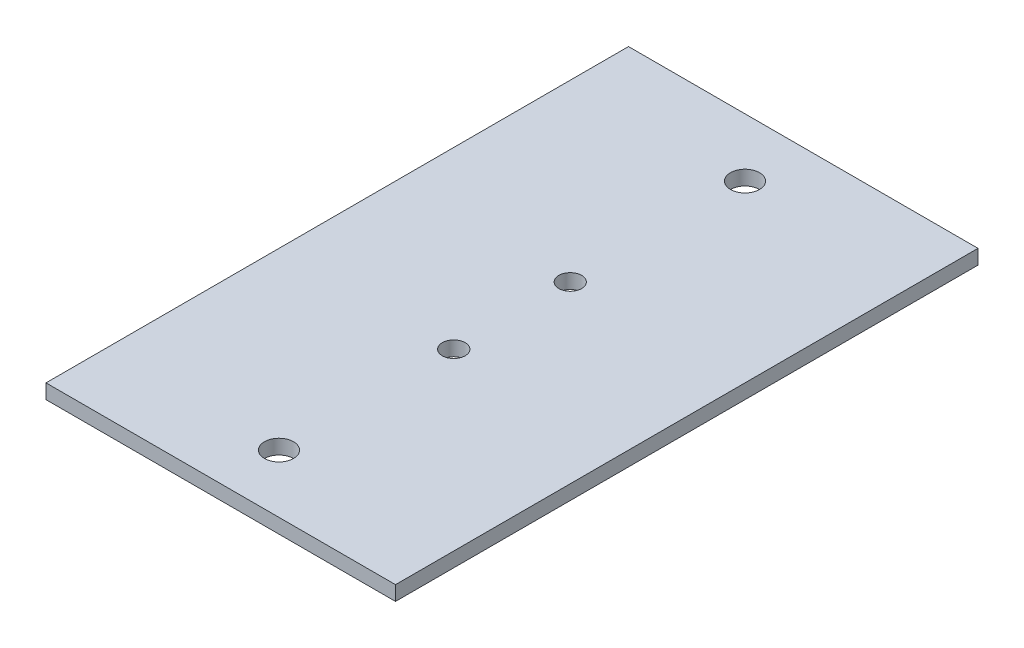
SolidWorks part; units mm, degrees
ref_plane "Front" through (0, 0, 0) normal (0, 0, 1) x (1, 0, 0)
ref_plane "Top" through (0, 0, 0) normal (0, 1, 0) x (1, 0, 0)
ref_plane "Right" through (0, 0, 0) normal (1, 0, 0) x (0, 0, -1)
sketch "Sketch1" plane through (0, 0, 0) normal (0, 0, 1) x (1, 0, 0)
  line L0 (0, 0) -> (76.2, 0)
  dimension "D1" = 76.2
extrude "Extrude-Thin1" add sketch "Sketch1" along normal blind 127 thin
sketch "Sketch2" plane through (0, 0, 0) normal (0, 1, 0) x (1, 0, 0)
  line L0 (38.1, -127) -> (38.1, 0) construction
  line L1 (0, -127) -> (76.2, -127) construction
  line L2 (0, 0) -> (76.2, 0) construction
  circle A0 centre (38.1, -12.7) radius 3.175
  circle A1 centre (38.1, -50.8) radius 2.4892
  circle A2 centre (38.1, -76.2) radius 2.4892
  circle A3 centre (38.1, -114.3) radius 3.175
  dimension "D1" = 6.35
  dimension "D2" = 4.9784
  dimension "D3" = 12.7
  dimension "D4" = 12.7
  dimension "D5" = 25.4
  dimension "D6" = 38.1
extrude "Cut-Extrude1" cut sketch "Sketch2" against normal through all
